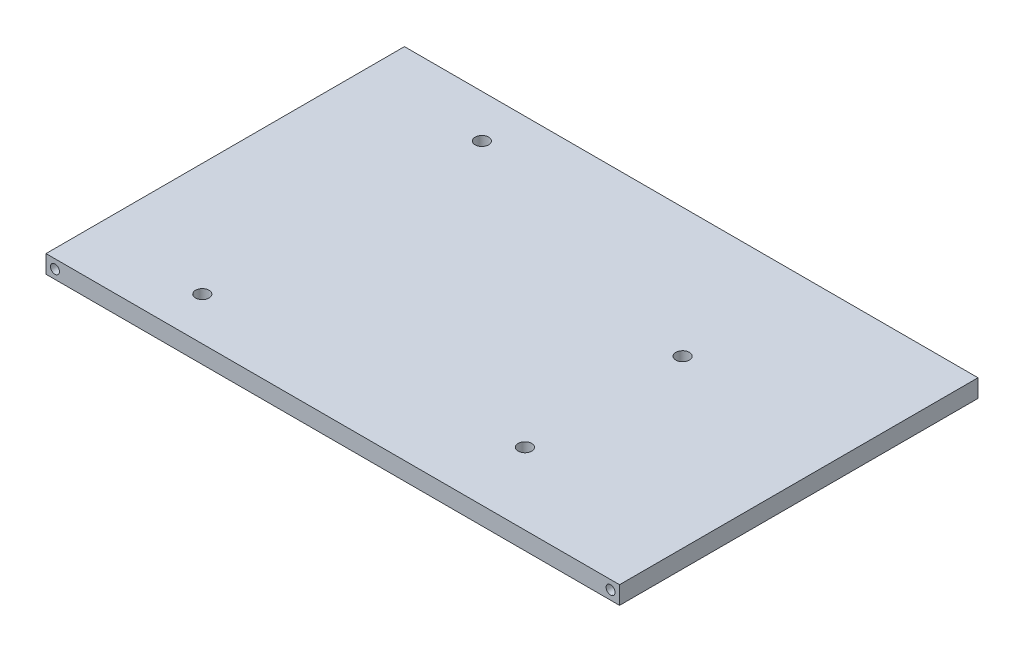
SolidWorks part; units mm, degrees
material "Acrylic (Medium-high impact)"
ref_plane "Front Plane" through (0, 0, 0) normal (0, 0, 1) x (1, 0, 0)
ref_plane "Top Plane" through (0, 0, 0) normal (0, 1, 0) x (1, 0, 0)
ref_plane "Right Plane" through (0, 0, 0) normal (1, 0, 0) x (0, 0, -1)
sketch "Sketch1" plane through (0, 0, 0) normal (0, 1, 0) x (1, 0, 0)
  line L1 (-42.2044, 20.6541) -> (59.3956, 20.6541)
  line L2 (-42.2044, 20.6541) -> (-42.2044, -42.8459)
  line L3 (-42.2044, -42.8459) -> (59.3956, -42.8459)
  line L4 (59.3956, 20.6541) -> (59.3956, -42.8459)
  dimension "D1" = 101.6
  dimension "D2" = 63.5
extrude "Boss-Extrude1" add sketch "Sketch1" along normal blind 3.175
sketch "Sketch2" plane through (0, 0, 42.8459) normal (0, 0, 1) x (1, 0, 0)
  line L0 (-42.2044, 3.175) -> (59.3956, 3.175) construction
  line L1 (-42.2044, 3.175) -> (-42.2044, 0) construction
  line L2 (59.3956, 3.175) -> (59.3956, 0) construction
  circle A0 centre (-40.6169, 1.5875) radius 0.7937
  circle A1 centre (57.8081, 1.5875) radius 0.7937
  dimension "D1" = 1.5875
  dimension "D4" = 1.5875
  dimension "D2" = 1.5875
  dimension "D3" = 1.5875
  dimension "D5" = 1.5875
  dimension "D6" = 1.5875
extrude "Cut-Extrude1" cut sketch "Sketch2" against normal blind 6.35
sketch "Sketch3" plane through (0, 0, -20.6541) normal (0, 0, -1) x (-1, 0, 0)
  line L0 (-59.3956, 3.175) -> (-59.3956, 0) construction
  line L1 (-59.3956, 0) -> (42.2044, 0) construction
  line L2 (42.2044, 3.175) -> (42.2044, 0) construction
  line L3 (-59.3956, 3.175) -> (42.2044, 3.175) construction
  circle A0 centre (-57.8081, 1.5875) radius 0.7937
  circle A1 centre (40.6169, 1.5875) radius 0.7937
  point P4 (-59.3956, 1.5875)
  point P9 (42.2044, 1.5875)
  dimension "D1" = 1.5875
  dimension "D3" = 1.5875
  dimension "D4" = 1.5875
  dimension "D2" = 1.5875
  dimension "D5" = 1.5875
  dimension "D6" = 1.5875
extrude "Cut-Extrude2" cut sketch "Sketch3" against normal blind 6.35
sketch "Sketch4" plane through (0, 3.175, 0) normal (0, 1, 0) x (1, 0, 0)
  line L0 (-42.2044, 20.6541) -> (-42.2044, -42.8459) construction
  line L1 (-42.2044, -42.8459) -> (59.3956, -42.8459) construction
  circle A0 centre (-20.8684, 13.0341) radius 1.1976
  circle A1 centre (-22.1384, -35.2259) radius 1.1976
  circle A2 centre (29.9316, -2.2059) radius 1.1976
  circle A3 centre (29.9316, -30.1459) radius 1.1976
  dimension "D1" = 2.3952
  dimension "D2" = 2.3952
  dimension "D3" = 2.3952
  dimension "D4" = 2.3952
  dimension "D5" = 21.336
  dimension "D6" = 20.066
  dimension "D7" = 48.26
  dimension "D8" = 7.62
  dimension "D9" = 50.8
  dimension "D10" = 50.8
  dimension "D11" = 15.24
  dimension "D12" = 27.94
extrude "Cut-Extrude3" cut sketch "Sketch4" against normal through all
